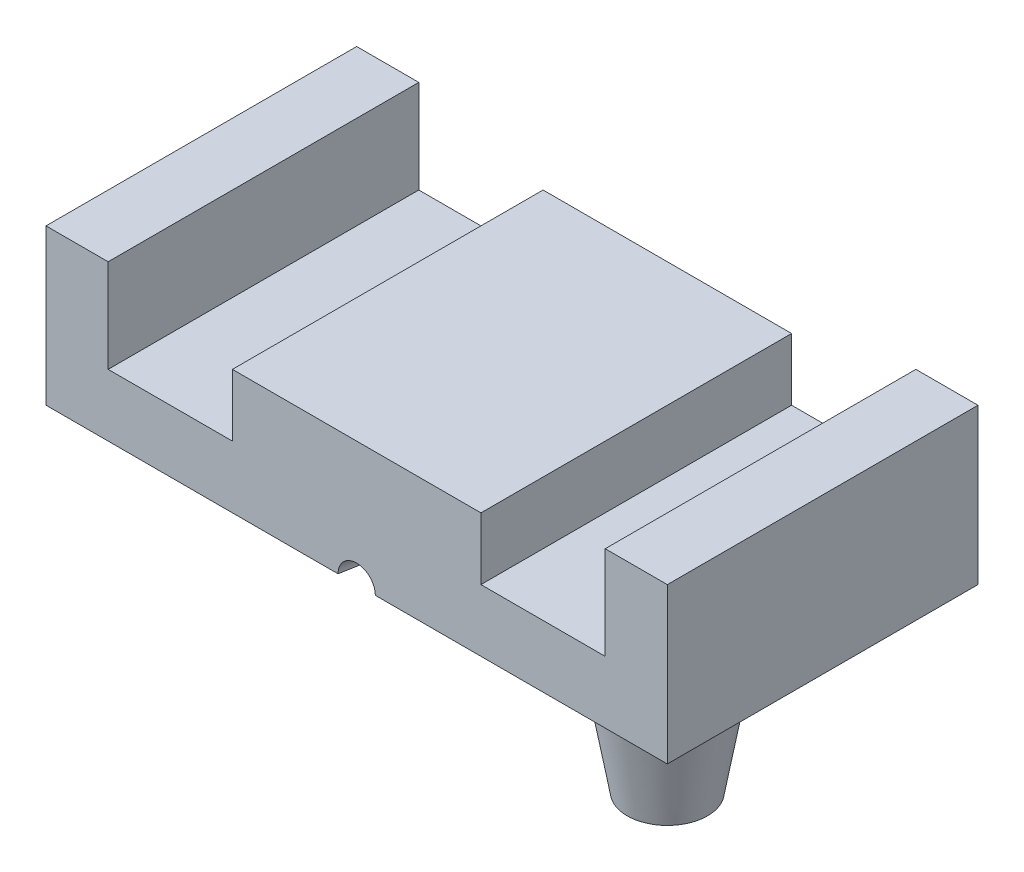
SolidWorks part; units mm, degrees
ref_plane "Plan de face" through (0, 0, 0) normal (0, 0, 1) x (1, 0, 0)
ref_plane "Plan de dessus" through (0, 0, 0) normal (0, 1, 0) x (1, 0, 0)
ref_plane "Plan de droite" through (0, 0, 0) normal (1, 0, 0) x (0, 0, -1)
sketch "Esquisse1" plane through (0, 0, 0) normal (0, 1, 0) x (1, 0, 0)
  line L1 (25, -12.5) -> (-25, -12.5)
  line L2 (25, -12.5) -> (25, 12.5)
  line L3 (25, 12.5) -> (-25, 12.5)
  line L4 (-25, -12.5) -> (-25, 12.5)
  dimension "D1" = 25
  dimension "D2" = 12.5
  dimension "D3" = 50
  dimension "D4" = 25
extrude "Boss.-Extru.1" add sketch "Esquisse1" against normal blind 12.5
sketch "Esquisse2" plane through (0, -12.5, 0) normal (0, -1, 0) x (1, 0, 0)
  line L0 (-25, 12.5) -> (25, 12.5) construction
  line L3 (25, 12.5) -> (25, -12.5) construction
  circle A0 centre (17, 4.5) radius 5
  dimension "D3" = 10
  dimension "D5" = 8
  dimension "D1" = 8
extrude "Boss.-Extru.2" add sketch "Esquisse2" along normal blind 10 draft 10 contours A0
sketch "Esquisse4" plane through (0, -12.5, 0) normal (0, -1, 0) x (1, 0, 0)
  line L1 (-25, -12.5) -> (-25, 12.5) construction
  line L2 (25, -12.5) -> (-25, -12.5) construction
  circle A0 centre (-17, -4.5) radius 5
  circle A1 centre (-17, -4.5) radius 3
  dimension "D3" = 10
  dimension "D4" = 6
  dimension "D1" = 8
  dimension "D2" = 8
extrude "Boss.-Extru.3" add sketch "Esquisse4" along normal blind 10 draft 10 contours A0
sketch "Esquisse6" plane through (0, 0, 0) normal (0, 0, 1) x (1, 0, 0)
  line L0 (0, -20) -> (0, -5)
  line L2 (25, -12.5) -> (-25, -12.5) construction
  arc A0 (0, -20) -> (0, -5) centre (0, -12.5) cw
  dimension "D1" = 7.5
ref_axis "Axe1" [suppressed] through (0, -20, 0) along (0, 1, 0)
revolve "Enlèvement de matière-Révolution1" cut sketch "Esquisse6" angle 360 about L0
sketch "Esquisse8" plane through (0, 0, 0) normal (0, 0, 1) x (1, 0, 0)
  line L0 (25, -12.5) -> (-25, -12.5) construction
  line L1 (8, -12.5) -> (10, -12.5)
  arc A0 (10, -12.5) -> (8, -12.5) centre (9, -12.5) ccw
  dimension "D1" = 1
  dimension "D2" = 9
revolve "Enlèvement de matière-Révolution2" cut sketch "Esquisse8" angle 360 about axis through (0, -20, 0) along (0, 1, 0)
sketch "Esquisse13" plane through (0, 0, -12.5) normal (0, 0, -1) x (-1, 0, 0)
  line L0 (20, 0) -> (20, -7.5)
  line L1 (-25, 0) -> (25, 0) construction
  line L2 (20, -7.5) -> (10, -7.5)
  line L3 (10, -7.5) -> (10, -2.5)
  line L4 (10, -2.5) -> (-10, -2.5)
  line L5 (-10, -2.5) -> (-10, -7.5)
  line L6 (-10, -7.5) -> (-20, -7.5)
  line L7 (-20, -7.5) -> (-20, 0)
  line L8 (25, -12.5) -> (25, 0) construction
  line L9 (-25, -12.5) -> (25, -12.5) construction
  line L10 (-25, -12.5) -> (-25, 0) construction
  line L11 (20, 0) -> (-20, 0)
  arc A0 (7.5, -12.5) -> (-7.5, -12.5) centre (0, -12.5) ccw construction
  dimension "D1" = 5
  dimension "D2" = 5
  dimension "D3" = 5
  dimension "D4" = 5
  dimension "D5" = 10
extrude "Enlèv. mat.-Extru.5" cut sketch "Esquisse13" against normal through all
sketch "Esquisse14" plane through (0, 0, 12.5) normal (0, 0, 1) x (1, 0, 0)
  line L0 (-25, -12.5) -> (25, -12.5) construction
  circle A0 centre (0, -12.5) radius 1.5
  dimension "D1" = 3
extrude "Enlèv. mat.-Extru.6" cut sketch "Esquisse14" against normal blind 4 draft 10
